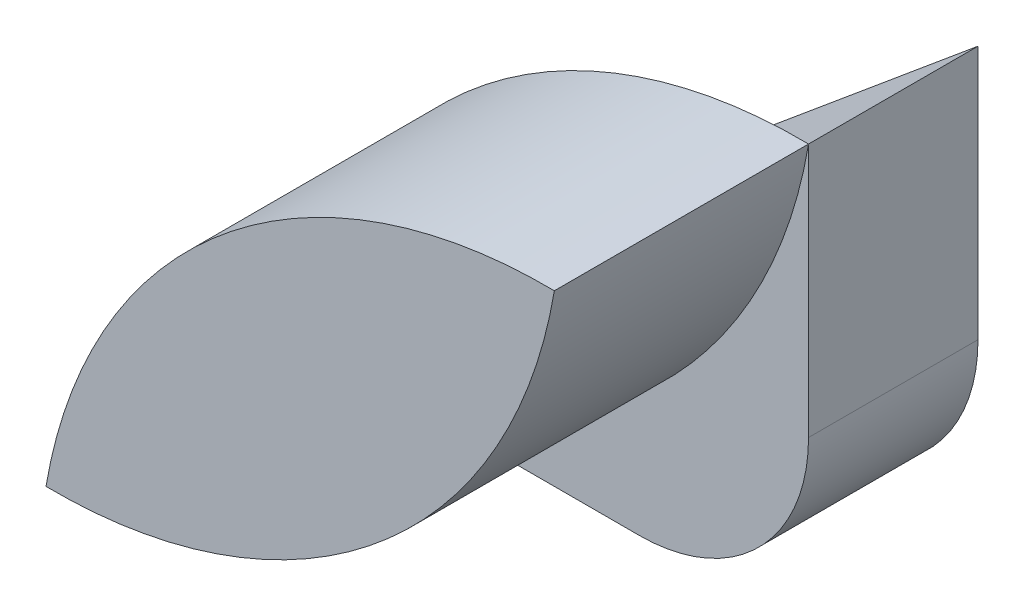
SolidWorks part; units mm, degrees
ref_plane "Front Plane" through (0, 0, 0) normal (0, 0, 1) x (1, 0, 0)
ref_plane "Top Plane" through (0, 0, 0) normal (0, 1, 0) x (1, 0, 0)
ref_plane "Right Plane" through (0, 0, 0) normal (1, 0, 0) x (0, 0, -1)
sketch "Sketch1" plane through (0, 0, 0) normal (0, 0, 1) x (1, 0, 0)
  line L0 (-30, -25) -> (0, 0)
  line L1 (0, 0) -> (0, -15)
  line L2 (-10, -25) -> (-30, -25)
  arc A0 (0, -15) -> (-10, -25) centre (-10, -15) cw
  dimension "D1" = 15
  dimension "D2" = 20
  dimension "D3" = 10
extrude "Boss-Extrude1" add sketch "Sketch1" along normal blind 10
sketch "Sketch3" plane through (0, 0, 10) normal (0, 0, 1) x (1, 0, 0)
  arc A0 (-30, -25) -> (0, 0) centre (-0.4191, -29.9971) cw
  arc A1 (-30, -25) -> (0, 0) centre (-29.5809, 4.9971) ccw
  dimension "D1" = 30
extrude "Boss-Extrude2" add sketch "Sketch3" along normal blind 15
